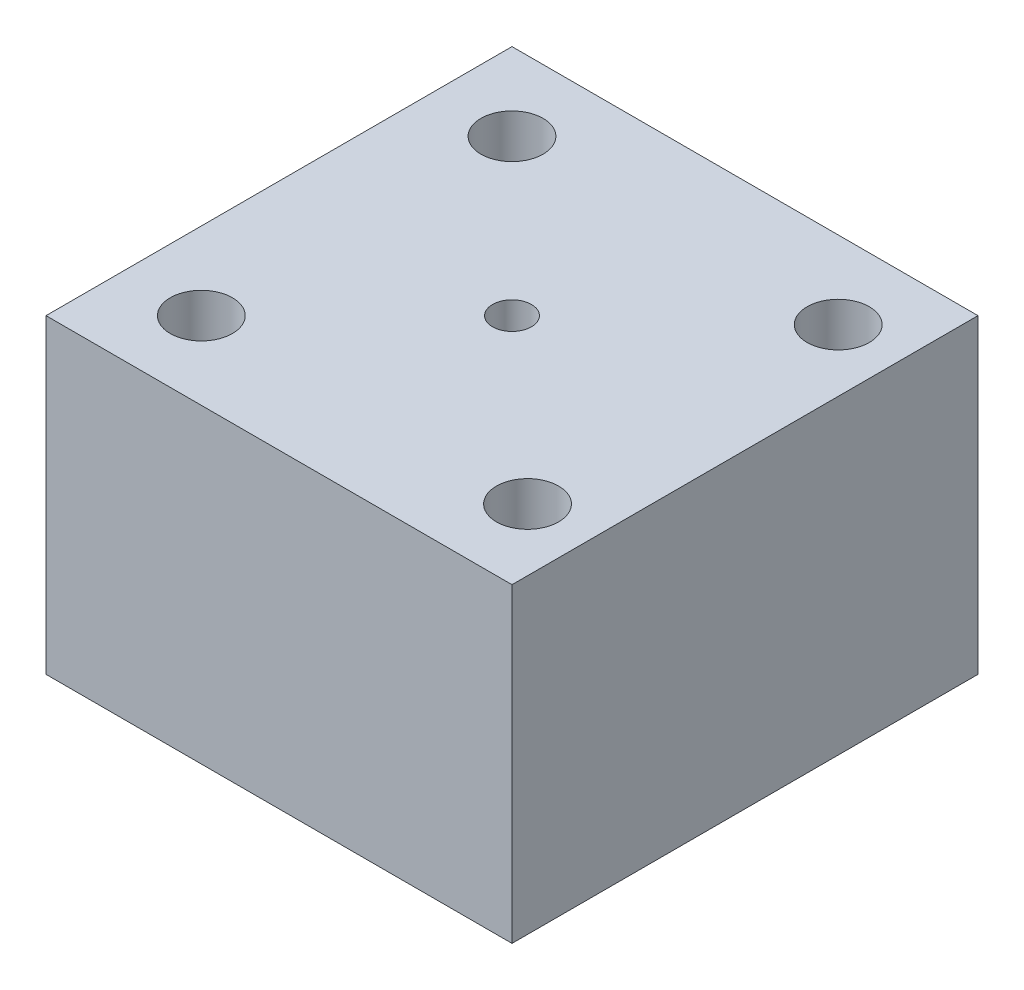
SolidWorks part; units mm, degrees
ref_plane "Front Plane" through (0, 0, 0) normal (0, 0, 1) x (1, 0, 0)
ref_plane "Top Plane" through (0, 0, 0) normal (0, 1, 0) x (1, 0, 0)
ref_plane "Right Plane" through (0, 0, 0) normal (1, 0, 0) x (0, 0, -1)
sketch "Sketch1" plane through (0, 0, 0) normal (0, 1, 0) x (1, 0, 0)
  line L1 (0, 0) -> (30, 0)
  line L2 (0, 0) -> (0, 30)
  line L3 (0, 30) -> (30, 30)
  line L4 (30, 0) -> (30, 30)
  dimension "D1" = 30
  dimension "D2" = 30
extrude "Boss-Extrude1" add sketch "Sketch1" along normal blind 20
sketch "Sketch2" plane through (0, 20, 0) normal (0, 1, 0) x (1, 0, 0)
  line L0 (30, 30) -> (0, 30) construction
  line L1 (0, 30) -> (0, 0) construction
  line L2 (0, 0) -> (30, 0) construction
  line L3 (30, 0) -> (30, 30) construction
  circle A0 centre (5, 25) radius 2
  circle A1 centre (5, 5) radius 2
  circle A2 centre (26, 5) radius 2
  circle A3 centre (26, 25) radius 2
  circle A4 centre (15, 15) radius 1.25
  dimension "D1" = 4
  dimension "D4" = 4
  dimension "D6" = 4
  dimension "D8" = 4
  dimension "D9" = 2.5
  dimension "D2" = 5
  dimension "D3" = 5
  dimension "D5" = 5
  dimension "D7" = 4
extrude "Cut-Extrude1" cut sketch "Sketch2" against normal blind 20
